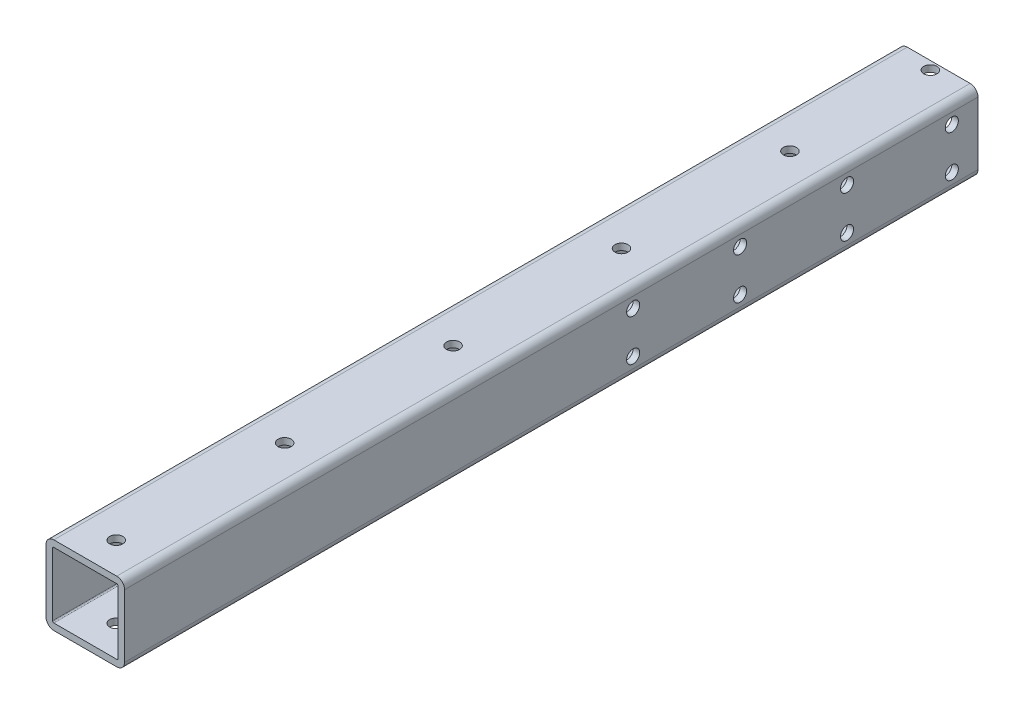
SolidWorks part; units mm, degrees
material "Alloy Steel"
ref_plane "Front Plane" through (0, 0, 0) normal (0, 0, 1) x (1, 0, 0)
ref_plane "Top Plane" through (0, 0, 0) normal (0, 1, 0) x (1, 0, 0)
ref_plane "Right Plane" through (0, 0, 0) normal (1, 0, 0) x (0, 0, -1)
sketch "Sketch1" plane through (0, 0, 0) normal (0, 0, 1) x (1, 0, 0)
  line L0 (-15.875, 15.875) -> (-15.875, -15.875)
  line L1 (-19.05, 19.05) -> (19.05, 19.05)
  line L2 (-19.05, 19.05) -> (-19.05, -19.05)
  line L3 (-19.05, -19.05) -> (19.05, -19.05)
  line L4 (19.05, 19.05) -> (19.05, -19.05)
  line L5 (-19.05, 19.05) -> (19.05, -19.05) construction
  line L6 (-19.05, -19.05) -> (19.05, 19.05) construction
  line L7 (-15.875, -15.875) -> (15.875, -15.875)
  line L8 (15.875, 15.875) -> (15.875, -15.875)
  line L9 (-15.875, 15.875) -> (15.875, 15.875)
  point P0 (0, 0)
  dimension "D2" = 38.1
  dimension "D3" = 38.1
  dimension "D1" = 3.175
extrude "Boss-Extrude1" add sketch "Sketch1" along normal mid plane 413.8
fillet "Fillet1" radius 3.81 4 edges at (-19.05, -19.05, 0) (19.05, -19.05, 0) (-19.05, 19.05, 0) (19.05, 19.05, 0)
fillet "Fillet2" radius 0.635 4 edges at (15.875, -15.875, 0) (15.875, 15.875, 0) (-15.875, 15.875, 0) (-15.875, -15.875, 0)
sketch "Sketch2" plane through (0, 19.05, 0) normal (0, 1, 0) x (1, 0, 0)
  line L0 (0, -206.9) -> (0, 206.9) construction
  line L1 (15.24, -206.9) -> (-15.24, -206.9) construction
  line L2 (15.24, 206.9) -> (-15.24, 206.9) construction
  circle A0 centre (0, 202.85) radius 3.175
  circle A1 centre (0, 134.75) radius 3.175
  circle A2 centre (0, 53.0875) radius 3.175
  circle A3 centre (0, -28.575) radius 3.175
  circle A4 centre (0, -110.2375) radius 3.175
  circle A5 centre (0, -191.9) radius 3.175
  dimension "D1" = 6.35
  dimension "D2" = 15
  dimension "D3" = 81.6625
  dimension "D4" = 81.6625
  dimension "D5" = 81.6625
  dimension "D6" = 81.6625
  dimension "D7" = 68.1
extrude "Cut-Extrude1" cut sketch "Sketch2" against normal through all both and the other way through all
sketch "Sketch3" plane through (19.05, 0, 0) normal (1, 0, 0) x (0, 0, -1)
  line L0 (206.9, 10.05) -> (-206.9, 10.05) construction
  line L1 (206.9, -15.24) -> (206.9, 15.24) construction
  line L2 (-206.9, -15.24) -> (-206.9, 15.24) construction
  line L3 (-206.9, -10.05) -> (206.9, -10.05) construction
  line L4 (-206.9, 19.05) -> (206.9, 19.05) construction
  line L5 (206.9, -19.05) -> (-206.9, -19.05) construction
  line L6 (20.955, 0) -> (-20.955, 0) construction
  circle A0 centre (194.2, 10.05) radius 3.175
  circle A1 centre (194.2, -10.05) radius 3.175
  circle A2 centre (143.4, 10.05) radius 3.175
  circle A3 centre (39.7, 10.05) radius 3.175
  circle A4 centre (91.55, 10.05) radius 3.175
  circle A5 centre (143.4, -10.05) radius 3.175
  circle A6 centre (91.55, -10.05) radius 3.175
  circle A7 centre (39.7, -10.05) radius 3.175
  point P22 (93.2762, 10.05)
  point P23 (124.2012, 10.05)
  point P24 (156.9453, 10.05)
  point P25 (46.9587, 10.05)
  dimension "D3" = 6.35
  dimension "D5" = 6.35
  dimension "D1" = 9
  dimension "D2" = 9
  dimension "D4" = 12.7
  dimension "D6" = 50.8
  dimension "D7" = 51.85
  dimension "D8" = 51.85
extrude "Cut-Extrude2" cut sketch "Sketch3" against normal through all
